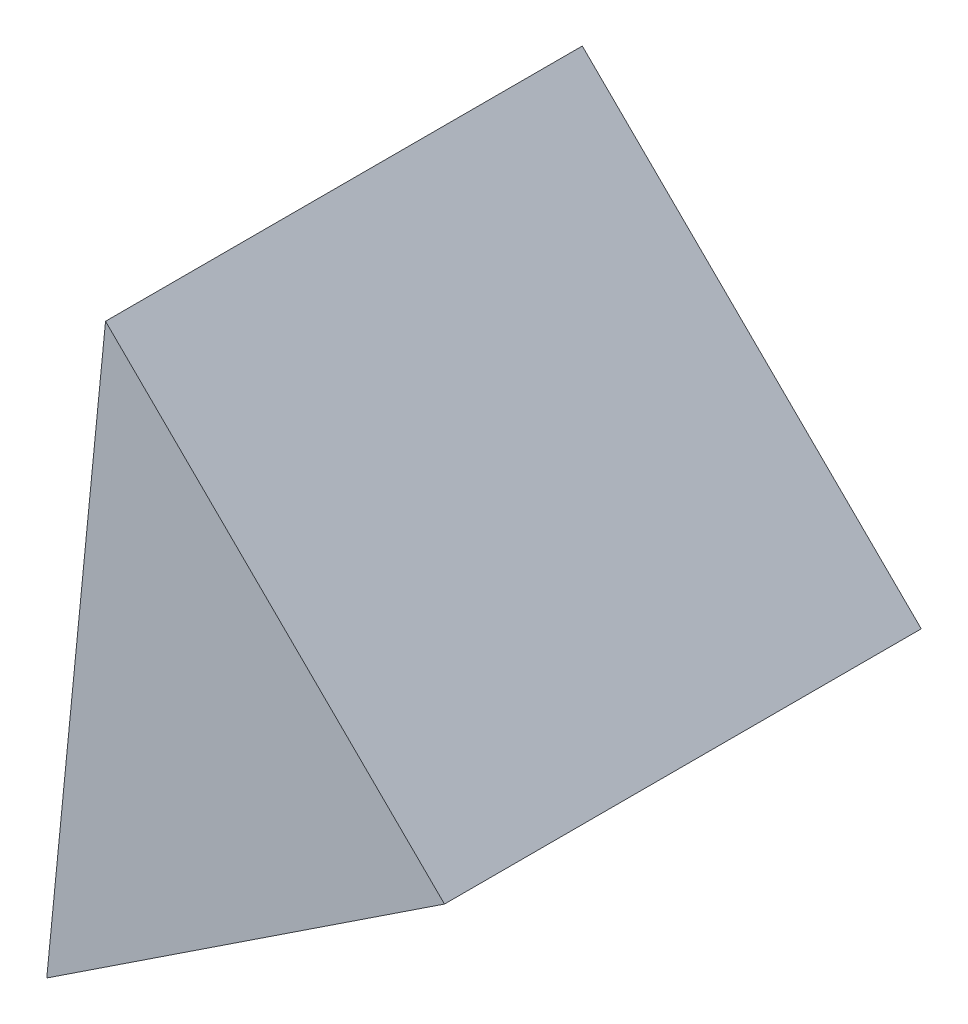
SolidWorks part; units mm, degrees
ref_plane "前视基准面" through (0, 0, 0) normal (0, 0, 1) x (1, 0, 0)
ref_plane "上视基准面" through (0, 0, 0) normal (0, 1, 0) x (1, 0, 0)
ref_plane "右视基准面" through (0, 0, 0) normal (1, 0, 0) x (0, 0, -1)
sketch "草图2" plane through (0, 0, 0) normal (0, 0, 1) x (1, 0, 0)
  line L0 (9.0286, 6.3615) -> (1.9188, 13.3937)
  line L1 (9.0286, 6.3615) -> (0.6862, 0.8475)
  line L2 (0.6862, 0.8475) -> (1.9188, 13.3937)
  dimension "D1" = 10
  dimension "D2" = 10
extrude "凸台-拉伸1" add sketch "草图2" along normal blind 10
